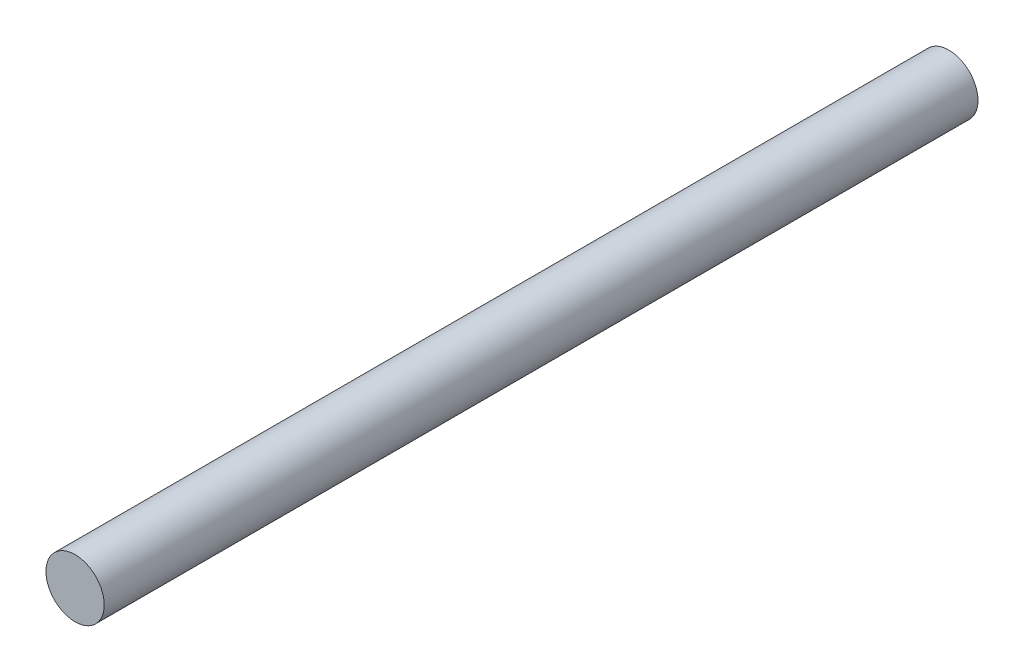
SolidWorks part; units mm, degrees
ref_plane "前视基准面" through (0, 0, 0) normal (0, 0, 1) x (1, 0, 0)
ref_plane "上视基准面" through (0, 0, 0) normal (0, 1, 0) x (1, 0, 0)
ref_plane "右视基准面" through (0, 0, 0) normal (1, 0, 0) x (0, 0, -1)
other "Configuration Table"
sketch "草图1" plane through (0, 0, 0) normal (0, 0, 1) x (1, 0, 0)
  circle A0 centre (0, 0) radius 5
  dimension "D1" = 10
extrude "凸台-拉伸1" add sketch "草图1" along normal blind 150
